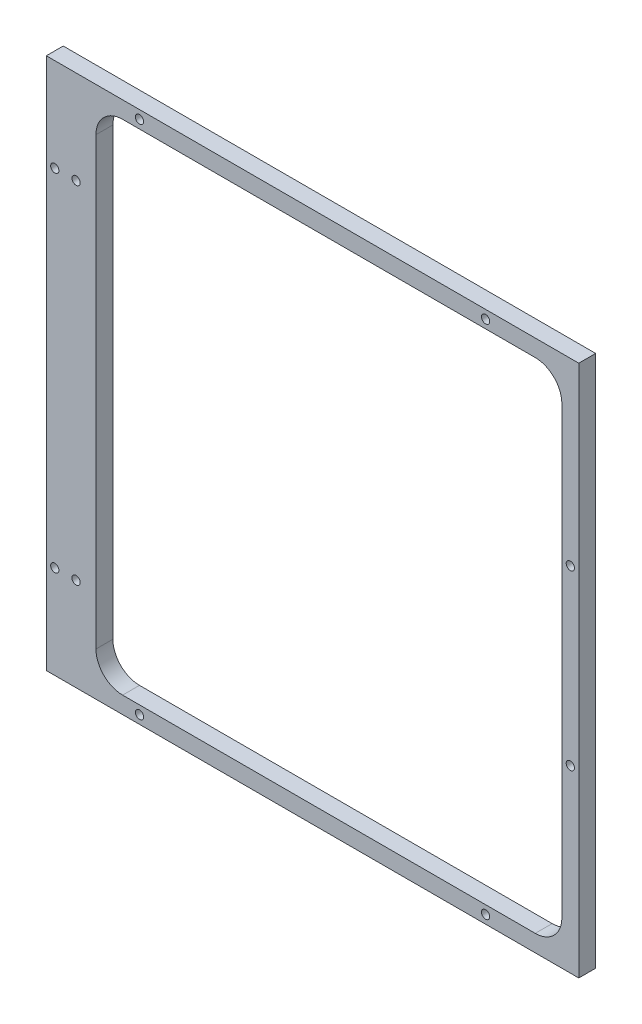
SolidWorks part; units mm, degrees
ref_plane "Front Plane" through (0, 0, 0) normal (0, 0, 1) x (1, 0, 0)
ref_plane "Top Plane" through (0, 0, 0) normal (0, 1, 0) x (1, 0, 0)
ref_plane "Right Plane" through (0, 0, 0) normal (1, 0, 0) x (0, 0, -1)
sketch "Sketch1" plane through (0, 0, 0) normal (0, 0, 1) x (1, 0, 0)
  line L1 (-100, -100) -> (100, -100)
  line L2 (-100, -100) -> (-100, 100)
  line L3 (-100, 100) -> (100, 100)
  line L4 (100, -100) -> (100, 100)
  line L5 (-100, -100) -> (100, 100) construction
  line L6 (-100, 100) -> (100, -100) construction
  point P0 (0, 0)
  dimension "D1" = 200
  dimension "D2" = 200
extrude "Boss-Extrude1" add sketch "Sketch1" along normal blind 6.35
sketch "Sketch2" plane through (0, 0, 6.35) normal (0, 0, 1) x (1, 0, 0)
  line L0 (100, -100) -> (100, 100) construction
  line L1 (83.65, 93.65) -> (-71.35, 93.65)
  line L2 (93.65, 83.65) -> (93.65, -83.65)
  line L3 (83.65, -93.65) -> (-71.35, -93.65)
  line L4 (-81.35, 83.65) -> (-81.35, -83.65)
  line L6 (100, 100) -> (-100, 100) construction
  line L7 (-100, -100) -> (100, -100) construction
  arc A0 (93.65, -83.65) -> (83.65, -93.65) centre (83.65, -83.65) cw
  arc A1 (83.65, 93.65) -> (93.65, 83.65) centre (83.65, 83.65) cw
  arc A2 (-71.35, 93.65) -> (-81.35, 83.65) centre (-71.35, 83.65) ccw
  arc A3 (-71.35, -93.65) -> (-81.35, -83.65) centre (-71.35, -83.65) cw
  point P14 (93.65, 93.65)
  point P17 (-81.35, 93.65)
  dimension "D5" = 10
  dimension "D1" = 6.35
  dimension "D2" = 175
  dimension "D3" = 6.35
  dimension "D4" = 6.35
extrude "Cut-Extrude1" cut sketch "Sketch2" against normal blind 6.35
sketch "Sketch3" plane through (0, 0, 6.35) normal (0, 0, 1) x (1, 0, 0)
  line L0 (100, -100) -> (100, 100) construction
  line L1 (-100, 100) -> (100, 100) construction
  line L2 (-100, 100) -> (-100, -100) construction
  line L4 (100, 100) -> (100, -50) construction
  line L5 (0, -50) -> (0, 100) construction
  line L6 (6.15, 93.65) -> (6.15, 100) construction
  line L7 (93.65, 0) -> (100, 0) construction
  line L8 (-100, 0) -> (100, 0) construction
  line L9 (-100, 100) -> (-100, -100) construction
  line L12 (100, 100) -> (100, -50) construction
  line L13 (100, -50) -> (0, -50) construction
  line L19 (93.65, -83.65) -> (93.65, 83.65)
  line L20 (-71.35, -93.65) -> (83.65, -93.65)
  line L21 (-81.35, 83.65) -> (-81.35, -83.65)
  line L22 (83.65, 93.65) -> (-71.35, 93.65)
  line L23 (93.65, -83.65) -> (93.65, 83.65)
  line L24 (-71.35, -93.65) -> (83.65, -93.65)
  line L26 (83.65, 93.65) -> (-71.35, 93.65)
  line L29 (-81.35, 83.65) -> (-81.35, -83.65)
  circle A0 centre (-65, -96.825) radius 1.55
  circle A1 centre (65, -96.825) radius 1.55
  circle A2 centre (65, 96.825) radius 1.55
  circle A3 centre (-65, 96.825) radius 1.55
  circle A4 centre (96.825, 32.5) radius 1.55
  circle A5 centre (96.825, -32.5) radius 1.55
  circle A7 centre (-96.825, 65) radius 1.55
  circle A8 centre (-88.825, 65) radius 1.55
  circle A10 centre (-96.825, -65) radius 1.55
  circle A11 centre (-88.825, -65) radius 1.55
  arc A14 (83.65, -93.65) -> (93.65, -83.65) centre (83.65, -83.65) ccw
  arc A15 (-81.35, -83.65) -> (-71.35, -93.65) centre (-71.35, -83.65) ccw
  arc A16 (-81.35, -83.65) -> (-71.35, -93.65) centre (-71.35, -83.65) ccw
  arc A17 (93.65, 83.65) -> (83.65, 93.65) centre (83.65, 83.65) ccw
  arc A18 (83.65, -93.65) -> (93.65, -83.65) centre (83.65, -83.65) ccw
  arc A21 (93.65, 83.65) -> (83.65, 93.65) centre (83.65, 83.65) ccw
  arc A22 (-71.35, 93.65) -> (-81.35, 83.65) centre (-71.35, 83.65) ccw
  arc A23 (-71.35, 93.65) -> (-81.35, 83.65) centre (-71.35, 83.65) ccw
  point P45 (6.15, 96.825)
  point P58 (96.825, 0)
  dimension "D1" = 3.1
  dimension "D3" = 3.1
  dimension "D10" = 3.1
  dimension "D2" = 65
  dimension "D4" = 32.5
  dimension "D5" = 8
  dimension "D7" = 65
  dimension "D8" = 65
  dimension "D9" = 7.475
  dimension "D6" = 0
extrude "Cut-Extrude2" cut sketch "Sketch3" against normal up to surface (6.35 mm away) up to face at (6.15, 0, 0)
